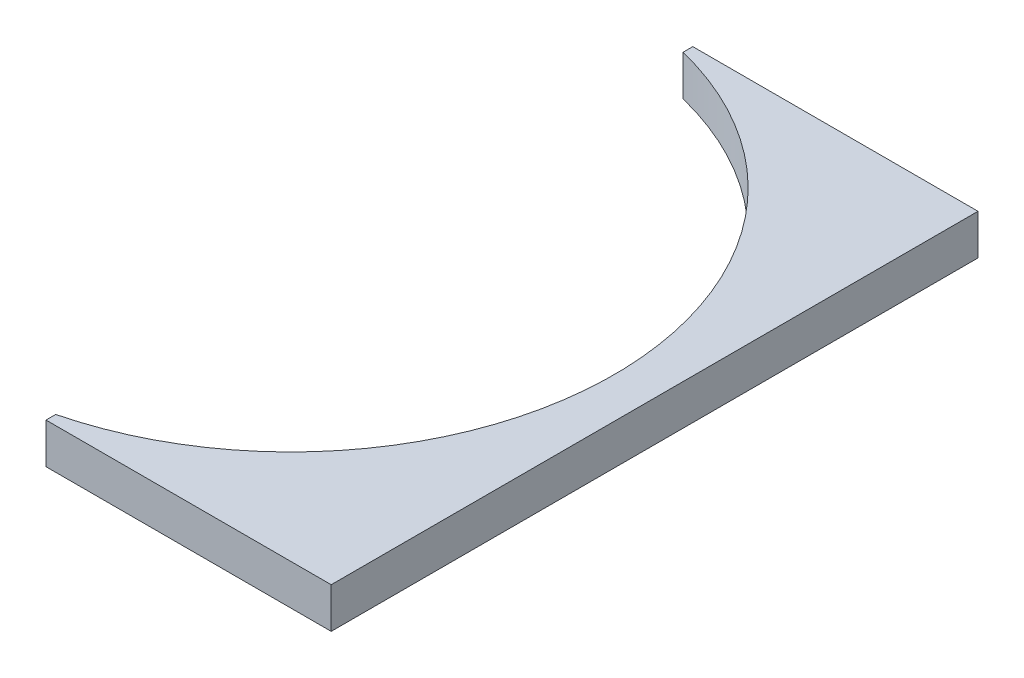
SolidWorks part; units mm, degrees
ref_plane "Front Plane" through (0, 0, 0) normal (0, 0, 1) x (1, 0, 0)
ref_plane "Top Plane" through (0, 0, 0) normal (0, 1, 0) x (1, 0, 0)
ref_plane "Right Plane" through (0, 0, 0) normal (1, 0, 0) x (0, 0, -1)
sketch "Sketch1" plane through (0, 0, 0) normal (0, 1, 0) x (1, 0, 0)
  line L4 (6.1749, 25.4) -> (28.575, 25.4)
  line L5 (28.575, 25.4) -> (28.575, -25.4)
  line L6 (28.575, -25.4) -> (6.1749, -25.4)
  line L7 (6.1749, -25.4) -> (6.1749, -24.638)
  line L8 (6.1749, 25.4) -> (6.1749, 24.638)
  line L9 (0, 0) -> (0, 25.4) construction
  circle A2 centre (0, 0) radius 25.4
  point P5 (0, 0)
  point P12 (0, 0)
  dimension "D1" = 50.8
  dimension "D2" = 0.762
  dimension "D3" = 0.762
  dimension "D4" = 28.575
extrude "Boss-Extrude1" add sketch "Sketch1" along normal blind 3.175 contours A2 L7 L6 L5 L4 L8
